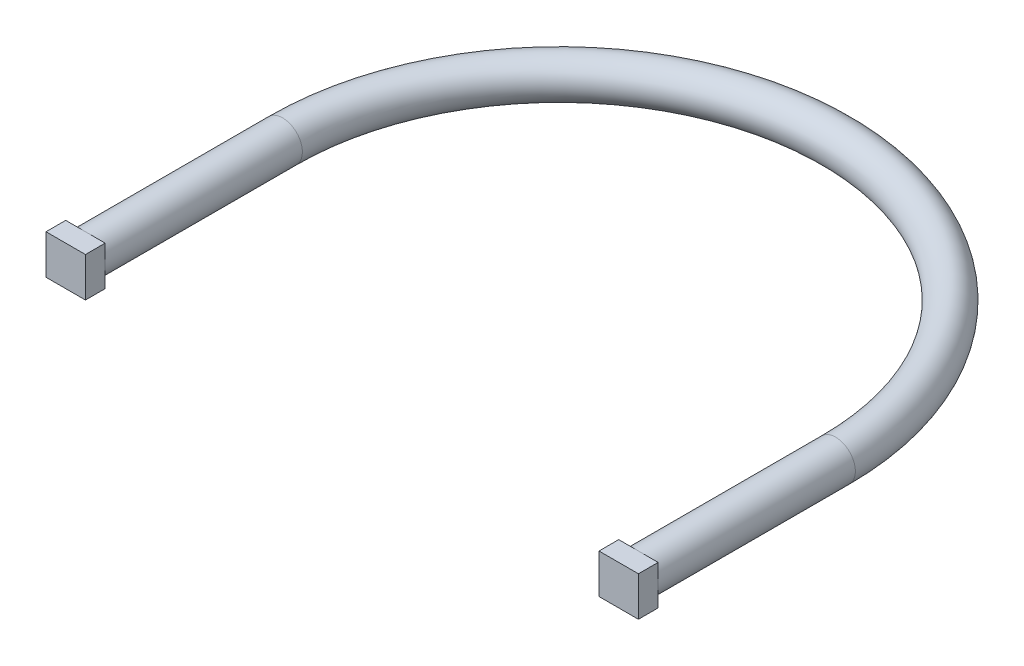
SolidWorks part; units mm, degrees
ref_plane "Front Plane" through (0, 0, 0) normal (0, 0, 1) x (1, 0, 0)
ref_plane "Top Plane" through (0, 0, 0) normal (0, 1, 0) x (1, 0, 0)
ref_plane "Right Plane" through (0, 0, 0) normal (1, 0, 0) x (0, 0, -1)
sketch "Sketch6" plane through (0, 0, 0) normal (0, 0, 1) x (1, 0, 0)
  circle A0 centre (0, 0) radius 5
  dimension "D1" = 10
sketch "Sketch7" plane through (0, 0, 0) normal (0, 1, 0) x (1, 0, 0)
  line L0 (0, 0) -> (0, 50)
  line L1 (140.2, 50) -> (140.2, 0)
  arc A0 (140.2, 50) -> (0, 50) centre (70.1, 50) ccw
  dimension "D1" = 140.2
  dimension "D2" = 50
  dimension "D3" = 50
sweep "Sweep1" add profiles "Sketch6" path "Sketch7"
sketch "Sketch8" plane through (0, 0, 0) normal (0, 0, 1) x (1, 0, 0)
  line L0 (-5, 5) -> (5, 5)
  line L2 (5, 5) -> (5, -5)
  line L3 (5, -5) -> (-5, -5)
  line L4 (-5, -5) -> (-5, 5)
  point P3 (-14.0331, 0.3256)
  dimension "D1" = 5
  dimension "D2" = 5
  dimension "D3" = 5
  dimension "D4" = 5
extrude "Boss-Extrude1" add sketch "Sketch8" along normal blind 5
sketch "Sketch9" plane through (0, 0, 0) normal (0, 0, 1) x (1, 0, 0)
  line L0 (5, -5) -> (5, 5) construction
  line L1 (135.2, -5) -> (145.2, -5)
  line L2 (135.2, -5) -> (135.2, 5)
  line L3 (135.2, 5) -> (145.2, 5)
  line L4 (145.2, -5) -> (145.2, 5)
  line L5 (5, 5) -> (-5, 5) construction
  circle A6 centre (140.2, 0) radius 5 construction
  dimension "D1" = 5
extrude "Boss-Extrude2" add sketch "Sketch9" along normal blind 5
